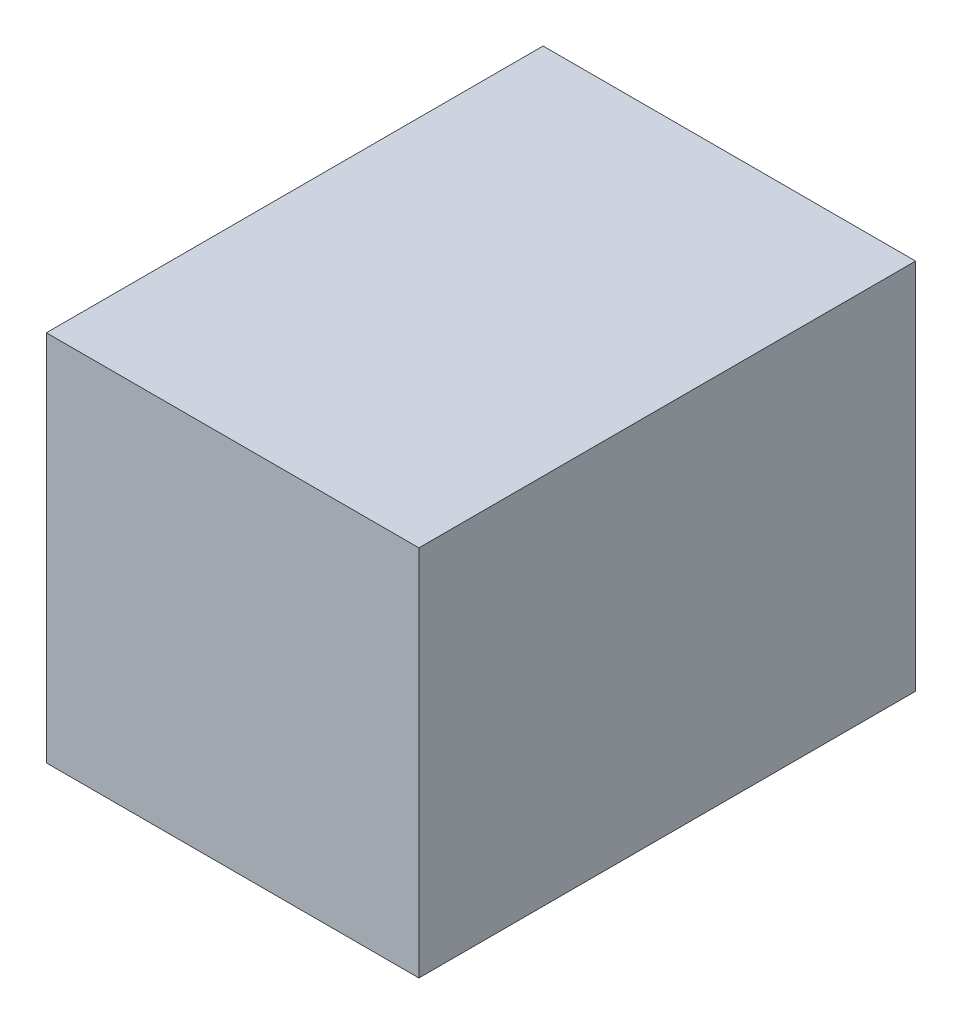
SolidWorks part; units mm, degrees
ref_plane "Front Plane" through (0, 0, 0) normal (0, 0, 1) x (1, 0, 0)
ref_plane "Top Plane" through (0, 0, 0) normal (0, 1, 0) x (1, 0, 0)
ref_plane "Right Plane" through (0, 0, 0) normal (1, 0, 0) x (0, 0, -1)
sketch "Sketch1" plane through (0, 0, 0) normal (0, 0, 1) x (1, 0, 0)
  line L1 (0, 0) -> (76.2, 0)
  line L2 (0, 0) -> (0, 76.2)
  line L3 (0, 76.2) -> (76.2, 76.2)
  line L4 (76.2, 0) -> (76.2, 76.2)
  dimension "D1" = 76.2
extrude "Boss-Extrude1" add sketch "Sketch1" along normal blind 101.6
